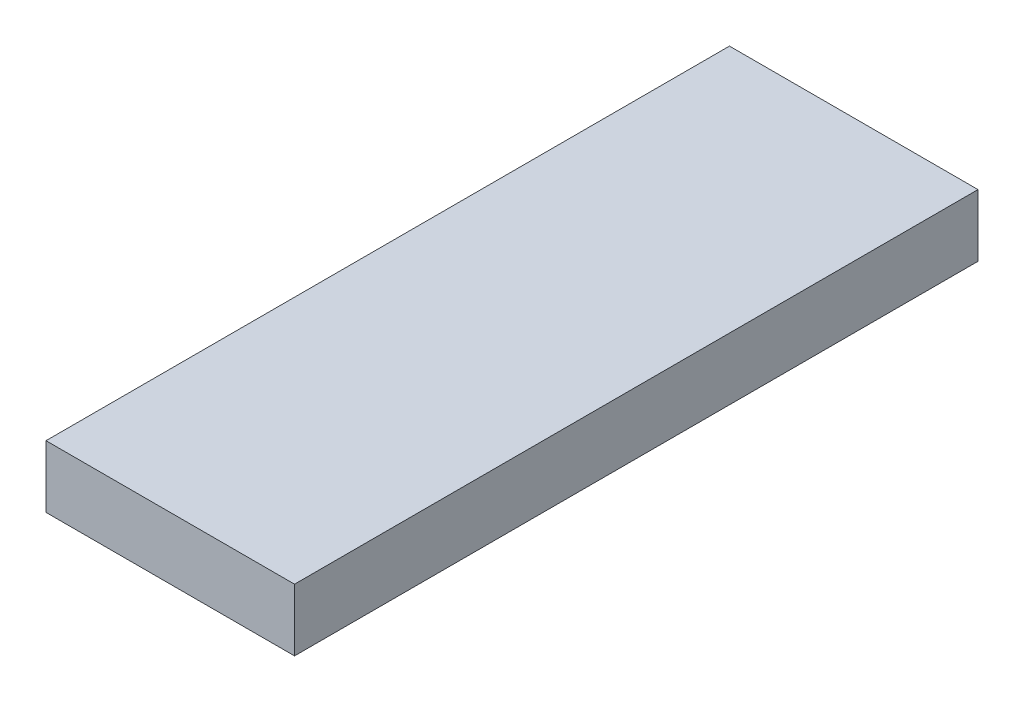
SolidWorks part; units mm, degrees
ref_plane "Front Plane" through (0, 0, 0) normal (0, 0, 1) x (1, 0, 0)
ref_plane "Top Plane" through (0, 0, 0) normal (0, 1, 0) x (1, 0, 0)
ref_plane "Right Plane" through (0, 0, 0) normal (1, 0, 0) x (0, 0, -1)
sketch "Sketch1" plane through (0, 0, 0) normal (0, 1, 0) x (1, 0, 0)
  line L1 (-20, 55) -> (20, 55)
  line L2 (-20, 55) -> (-20, -55)
  line L3 (-20, -55) -> (20, -55)
  line L4 (20, 55) -> (20, -55)
  line L5 (-20, 55) -> (20, -55) construction
  line L6 (-20, -55) -> (20, 55) construction
  point P0 (0, 0)
  dimension "D1" = 110
  dimension "D2" = 40
extrude "Boss-Extrude1" add sketch "Sketch1" along normal blind 10
